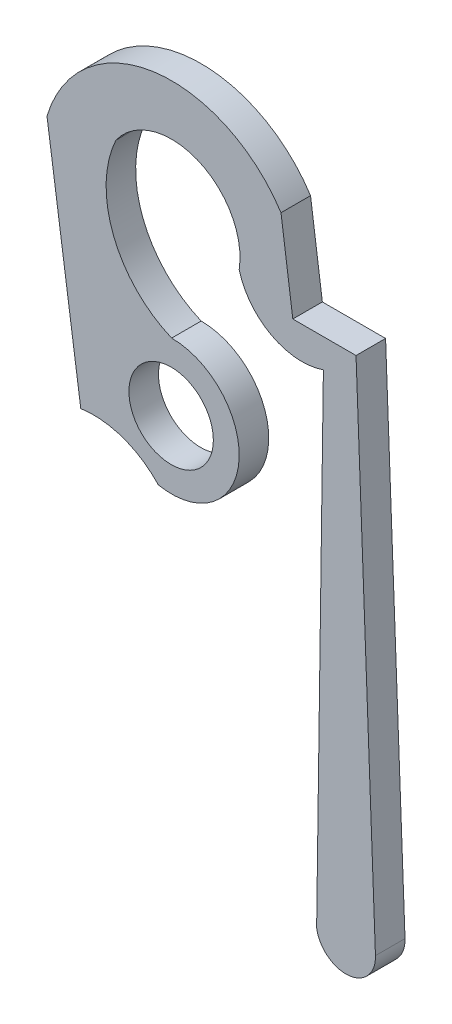
SolidWorks part; units mm, degrees
material "AISI 4340 Steel, normalized"
ref_plane "Front Plane" through (0, 0, 0) normal (0, 0, 1) x (1, 0, 0)
ref_plane "Top Plane" through (0, 0, 0) normal (0, 1, 0) x (1, 0, 0)
ref_plane "Right Plane" through (0, 0, 0) normal (1, 0, 0) x (0, 0, -1)
sketch "Sketch1" plane through (0, 0, 0) normal (0, 0, 1) x (1, 0, 0)
  line L0 (0.2144, 4.0365) -> (4.2844, 4.0365) construction
  line L1 (-33.8127, -4.8254) -> (30.8628, -4.8254) construction
  line L2 (-4.548, 7.9628) -> (-3.532, 0.8508)
  line L3 (2.4906, 8.9637) -> (2.8462, 6.3729)
  line L4 (2.8462, 6.3729) -> (4.7478, 6.3729)
  line L5 (4.7478, 6.3729) -> (5.332, -8.9687)
  line L7 (3.7659, 5.5081) -> (3.5627, -9.1223)
  arc A0 (2.4906, 8.9637) -> (-4.548, 7.9628) centre (-0.7989, 6.8471) ccw
  arc A1 (-3.532, 0.8508) -> (-1.1996, 0.029) centre (-3.151, -1.7889) cw
  arc A2 (-1.1996, 0.029) -> (-0.7989, 4.0531) centre (-0.7989, 2.0211) ccw
  arc A3 (-0.7989, 4.0531) -> (-2.4778, 8.3665) centre (0.4558, 7.0249) cw
  arc A4 (-2.4778, 8.3665) -> (1.2327, 6.8524) centre (-0.7989, 7.1773) cw
  arc A5 (1.2327, 6.8524) -> (3.7659, 5.5081) centre (3.1228, 7.3551) ccw
  arc A6 (3.5627, -9.1223) -> (5.332, -8.9687) centre (4.4436, -9.0025) ccw
  circle A7 centre (-0.8142, 2.0211) radius 1.27
  point P26 (0, 0)
  point P27 (0, 0)
  point P28 (0, 0)
  dimension "D1" = 3.81
  dimension "D2" = 2.032
  dimension "D3" = 2.667
  dimension "D4" = 2.3368
  dimension "D5" = 5.0038
  dimension "D6" = 5.1562
  dimension "D8" = 1.27
  dimension "D9" = 3.9116
  dimension "D10" = 2.0574
  dimension "D11" = 3.2258
  dimension "D13" = 1.016
  dimension "D15" = 0.3556
  dimension "D18" = 0.889
  dimension "D20" = 0.5842
  dimension "D21" = 14.6304
  dimension "D23" = 5.334
  dimension "D31" = 4.0365
  dimension "D7" = 4.826
  dimension "D16" = 11.0236
  dimension "D17" = 5.2578
  dimension "D24" = 3.937
  dimension "D25" = 1.9558
  dimension "D26" = 2.032
  dimension "D12" = 7.112
  dimension "D14" = 2.5908
  dimension "D19" = 15.3416
  dimension "D22" = 0.2032
  dimension "D32" = 4.8254
extrude "Boss-Extrude1" add sketch "Sketch1" along normal blind 0.889
